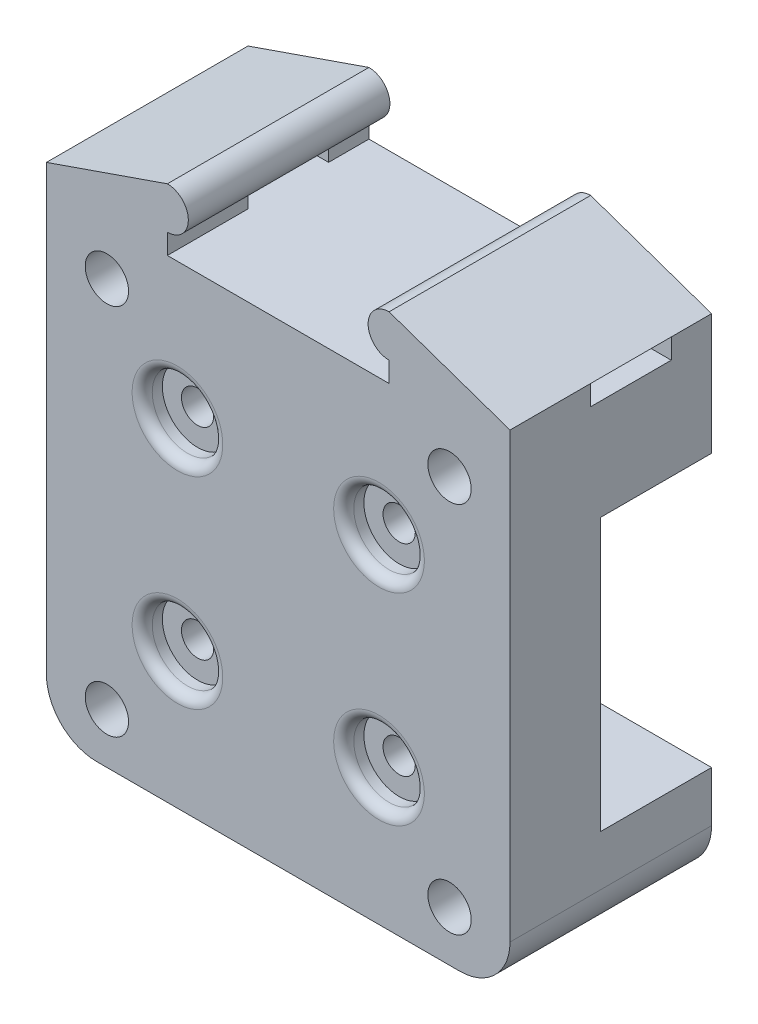
SolidWorks part; units mm, degrees
ref_plane "Front Plane" through (0, 0, 0) normal (0, 0, 1) x (1, 0, 0)
ref_plane "Top Plane" through (0, 0, 0) normal (0, 1, 0) x (1, 0, 0)
ref_plane "Right Plane" through (0, 0, 0) normal (1, 0, 0) x (0, 0, -1)
sketch "Sketch1" plane through (0, 0, 0) normal (0, 0, 1) x (1, 0, 0)
  line L5 (-23, -23.5) -> (23, -23.5)
  line L6 (-23, -23.5) -> (-23, 23.5)
  line L7 (-23, 23.5) -> (23, 23.5)
  line L8 (23, -23.5) -> (23, 23.5)
  line L9 (-23, -23.5) -> (23, 23.5) construction
  line L10 (-23, 23.5) -> (23, -23.5) construction
  point P0 (0, 0)
  dimension "D1" = 46
  dimension "D2" = 47
extrude "Boss-Extrude1" add sketch "Sketch1" along normal blind 9
sketch "Sketch2" plane through (0, 0, 9) normal (0, 0, 1) x (1, 0, 0)
  circle A0 centre (-10, 10) radius 1.6
  circle A3 centre (10, 10) radius 1.6
  circle A4 centre (-10, -10) radius 1.6
  circle A5 centre (10, -10) radius 1.6
  dimension "D1" = 3.2
  dimension "D2" = 10
  dimension "D3" = 10
  dimension "D4" = 2
  dimension "D5" = 2
extrude "Cut-Extrude1" cut sketch "Sketch2" against normal blind 10
sketch "Sketch3" plane through (0, 0, 0) normal (0, 0, 1) x (1, 0, 0)
  line L0 (23, -23.5) -> (23, 23.5) construction
  line L1 (23, 23.5) -> (-23, 23.5)
  line L2 (23, 23.5) -> (23, 13.5)
  line L3 (23, 13.5) -> (-23, 13.5)
  line L4 (-23, 23.5) -> (-23, 13.5)
  line L5 (-23, 23.5) -> (-23, -23.5) construction
  line L7 (23, -23.5) -> (-23, -23.5)
  line L8 (23, -23.5) -> (23, -13.5)
  line L9 (23, -13.5) -> (-23, -13.5)
  line L10 (-23, -23.5) -> (-23, -13.5)
  dimension "D1" = 13.5
  dimension "D2" = 10
  dimension "D3" = 10
extrude "Boss-Extrude2" add sketch "Sketch3" against normal blind 11
sketch "Sketch4" plane through (0, 0, 0) normal (0, 0, 1) x (1, 0, 0)
  line L0 (23, 23.5) -> (-23, 23.5) construction
  line L1 (-23, 23.5) -> (-23, -23.5) construction
  circle A0 centre (-17, 18.5) radius 2.15
  circle A1 centre (17, 18.5) radius 2.15
  circle A2 centre (-17, -18.5) radius 2.15
  circle A3 centre (17, -18.5) radius 2.15
  dimension "D1" = 4.3
  dimension "D5" = 2
  dimension "D2" = 5
  dimension "D3" = 6
  dimension "D6" = 34
  dimension "D7" = 37
  dimension "D4" = 2
extrude "Cut-Extrude2" cut sketch "Sketch4" against normal through all both and the other way through all
sketch "Sketch7" plane through (0, 0, -11) normal (0, 0, -1) x (-1, 0, 0)
  line L0 (0, 23.5) -> (0, 39.2593) construction
  line L4 (-23, 23.5) -> (23, 23.5) construction
  line L5 (-23, 23.5) -> (-11, 23.5)
  line L6 (-23, 23.5) -> (-23, 25.5)
  line L8 (-11, 23.5) -> (-11, 25.5)
  line L9 (-23, 25.5) -> (-11, 29.6593)
  line L10 (23, 23.5) -> (11, 23.5)
  line L11 (23, 23.5) -> (23, 25.5)
  line L12 (23, 25.5) -> (11, 29.6593)
  line L13 (11, 23.5) -> (11, 25.5)
  arc A2 (-11, 25.5) -> (-11, 29.6593) centre (-11, 27.5797) ccw
  arc A3 (11, 25.5) -> (11, 29.6593) centre (11, 27.5797) cw
  dimension "D1" = 2
  dimension "D2" = 2
  dimension "D3" = 2.0797
  dimension "D4" = 12
extrude "Boss-Extrude5" add sketch "Sketch7" against normal blind 20
sketch "Sketch8" plane through (0, 0, 0) normal (1, 0, 0) x (0, 0, -1)
  line L0 (-9, 23.5) -> (11, 23.5) construction
  line L1 (7, 23.5) -> (-1, 23.5)
  line L2 (7, 23.5) -> (7, 25.5)
  line L3 (7, 25.5) -> (-1, 25.5)
  line L4 (-1, 23.5) -> (-1, 25.5)
  line L5 (-9, 25.5) -> (11, 25.5) construction
  line L6 (11, 23.5) -> (11, 25.5) construction
  line L7 (-9, 23.5) -> (-9, 25.5) construction
  dimension "D1" = 4
  dimension "D2" = 8
extrude "Cut-Extrude3" cut sketch "Sketch8" against normal through all both and the other way through all
sketch "Sketch9" plane through (0, 0, 9) normal (0, 0, 1) x (1, 0, 0)
  circle A0 centre (-10, 10) radius 3.5
  circle A1 centre (10, 10) radius 3.5
  circle A2 centre (10, -10) radius 3.5
  circle A3 centre (-10, -10) radius 3.5
  dimension "D1" = 7
extrude "Cut-Extrude4" cut sketch "Sketch9" against normal blind 2
fillet "Fillet1" radius 1 4 edges at (-6.5, -10, 9) (13.5, -10, 9) (13.5, 10, 9) (-6.5, 10, 9)
fillet "Fillet2" radius 5 2 edges at (-23, -23.5, -1) (23, -23.5, -1)
sketch "Sketch10" plane through (0, 0, -11) normal (0, 0, -1) x (-1, 0, 0)
  circle A0 centre (-17, -18.5) radius 3.2
  circle A1 centre (17, -18.5) radius 3.2
  circle A2 centre (17, 18.5) radius 3.2
  circle A3 centre (-17, 18.5) radius 3.2
  dimension "D1" = 6.4
extrude "Cut-Extrude5" cut sketch "Sketch10" against normal blind 13
